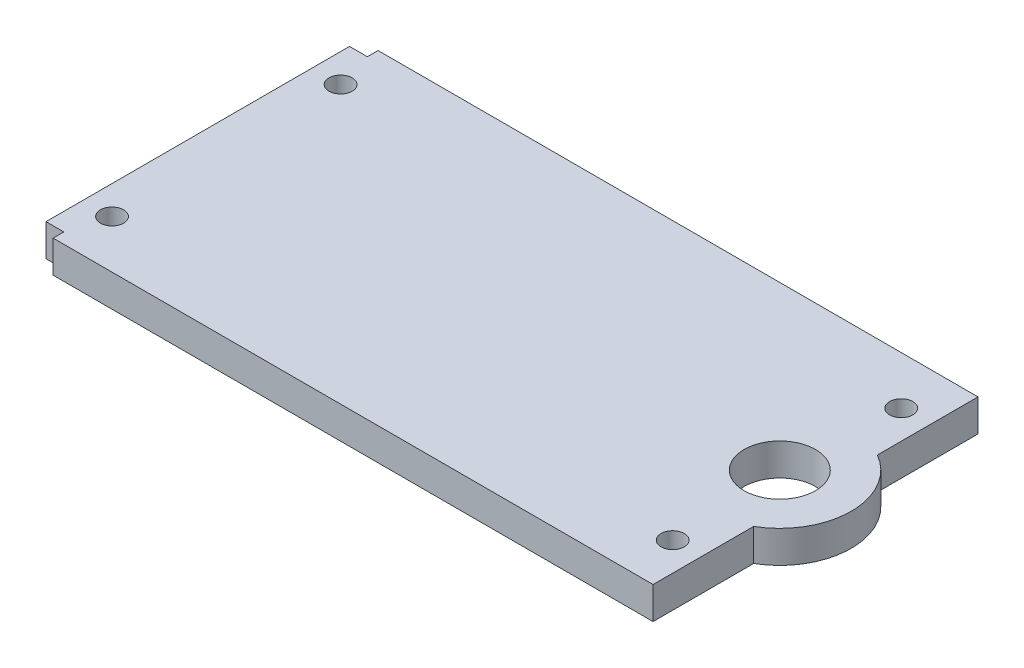
SolidWorks part; units mm, degrees
ref_plane "Front Plane" through (0, 0, 0) normal (0, 0, 1) x (1, 0, 0)
ref_plane "Top Plane" through (0, 0, 0) normal (0, 1, 0) x (1, 0, 0)
ref_plane "Right Plane" through (0, 0, 0) normal (1, 0, 0) x (0, 0, -1)
sketch "Sketch2" plane through (0, 0, 0) normal (0, 1, 0) x (1, 0, 0)
  line L0 (0, 0) -> (45, 0) construction
  line L1 (-41.5, -22.75) -> (45, -22.75)
  line L2 (-41.5, -22.75) -> (-41.5, 22.75)
  line L3 (-41.5, 22.75) -> (45, 22.75)
  line L4 (45, -22.75) -> (45, 22.75)
  dimension "D1" = 22.75
  dimension "D2" = 41.5
  dimension "D3" = 45
  dimension "D4" = 22.75
extrude "Boss-Extrude1" add sketch "Sketch2" along normal blind 4.5
sketch "Sketch3" plane through (0, 4.5, 0) normal (0, 1, 0) x (1, 0, 0)
  line L1 (-37.5, -16) -> (41, -16) construction
  line L2 (-37.5, -16) -> (-37.5, 16) construction
  line L3 (-37.5, 16) -> (41, 16) construction
  line L4 (41, -16) -> (41, 16) construction
  line L8 (0, 0) -> (0, 16) construction
  line L9 (0, 0) -> (0, -16) construction
  circle A0 centre (-37.5, -16) radius 1.625
  circle A1 centre (-37.5, 16) radius 1.625
  circle A2 centre (41, 16) radius 1.625
  circle A3 centre (41, -16) radius 1.625
  dimension "D5" = 3.25
  dimension "D1" = 16
  dimension "D2" = 37.5
  dimension "D3" = 41
extrude "Cut-Extrude1" cut sketch "Sketch3" against normal through all
sketch "Sketch5" plane through (0, 4.5, 0) normal (0, 1, 0) x (1, 0, 0)
  circle A0 centre (40, 0) radius 10
  dimension "D1" = 20
  dimension "D2" = 40
extrude "Boss-Extrude2" add sketch "Sketch5" against normal up to surface (4.5 mm away) up to face at (41, 0, 17.625)
sketch "Sketch6" plane through (0, 4.5, 0) normal (0, 1, 0) x (1, 0, 0)
  circle A0 centre (40, 0) radius 5
  arc A1 (45, -8.6603) -> (45, 8.6603) centre (40, 0) ccw construction
  dimension "D1" = 10
extrude "Cut-Extrude3" cut sketch "Sketch6" against normal through all
sketch "Sketch7" plane through (0, 4.5, 0) normal (0, 1, 0) x (1, 0, 0)
  line L1 (-41.5, 22.75) -> (-39, 22.75)
  line L2 (-41.5, 22.75) -> (-41.5, 21.25)
  line L3 (-41.5, 21.25) -> (-39, 21.25)
  line L4 (-39, 22.75) -> (-39, 21.25)
  line L5 (-41.5, -22.75) -> (-39, -22.75)
  line L6 (-41.5, -22.75) -> (-41.5, -21.25)
  line L7 (-41.5, -21.25) -> (-39, -21.25)
  line L8 (-39, -22.75) -> (-39, -21.25)
  dimension "D1" = 2.5
  dimension "D2" = 1.5
extrude "Cut-Extrude4" cut sketch "Sketch7" against normal through all
sketch "Sketch4" plane through (0, 4.5, 0) normal (0, 1, 0) x (1, 0, 0)
  line L0 (-7.5, -7.5) -> (7.5, 7.5) construction
  line L1 (-7.5, -7.5) -> (7.5, -7.5) construction
  line L2 (-7.5, -7.5) -> (-7.5, 7.5) construction
  line L3 (-7.5, 7.5) -> (7.5, 7.5) construction
  line L4 (7.5, -7.5) -> (7.5, 7.5) construction
  circle A0 centre (-7.5, -7.5) radius 1
  circle A1 centre (7.5, -7.5) radius 1
  circle A2 centre (7.5, 7.5) radius 1
  circle A3 centre (-7.5, 7.5) radius 1
  dimension "D1" = 2
  dimension "D2" = 15
  dimension "D3" = 15
